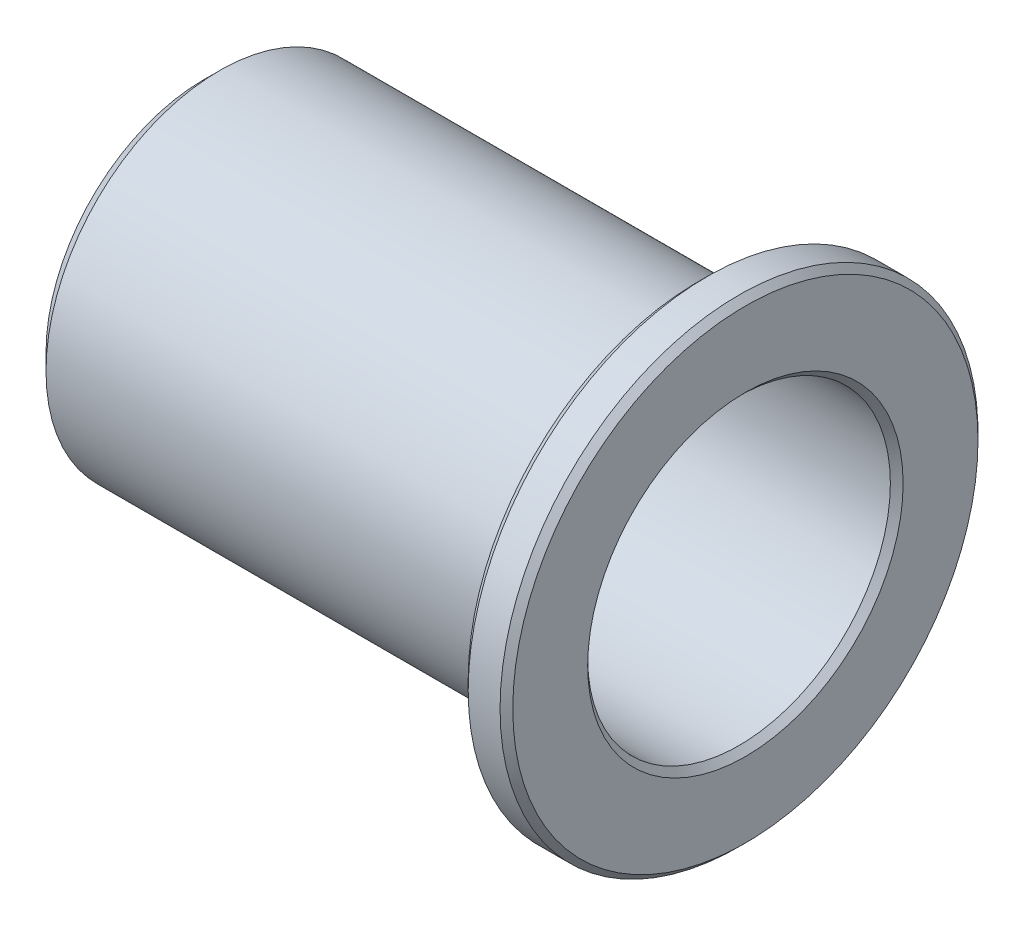
SolidWorks part; units mm, degrees
ref_plane "Спереди" through (0, 0, 0) normal (0, 0, 1) x (1, 0, 0)
ref_plane "Сверху" through (0, 0, 0) normal (0, 1, 0) x (1, 0, 0)
ref_plane "Справа" through (0, 0, 0) normal (1, 0, 0) x (0, 0, -1)
sketch "Эскиз1" plane through (0, 0, 0) normal (0, 0, 1) x (1, 0, 0)
  line L0 (-38.4825, 0) -> (53.8184, 0) construction
  line L18 (-31.1486, 4.75) -> (-31.1486, 4.95)
  line L19 (-14.1486, 4.95) -> (-14.1486, 7.3)
  line L20 (-30.6486, 5.45) -> (-15.6486, 5.45)
  line L21 (-15.6486, 5.45) -> (-15.6486, 7.2)
  line L22 (-15.3486, 7.5) -> (-14.3486, 7.5)
  line L23 (-31.1486, 4.75) -> (-14.3486, 4.75)
  line L24 (-31.1486, 4.95) -> (-30.6486, 5.45)
  line L25 (-15.6486, 7.2) -> (-15.3486, 7.5)
  line L26 (-14.1486, 7.3) -> (-14.3486, 7.5)
  line L27 (-14.3486, 4.75) -> (-14.1486, 4.95)
  point P4 (-31.1486, 5.45)
  point P7 (-14.1486, 7.5)
  point P11 (-15.6486, 7.5)
  point P12 (-14.1486, 4.75)
  dimension "D1" = 17
  dimension "D2" = 15
  dimension "D3" = 10.9
  dimension "D4" = 9.5
  dimension "D5" = 1.5
revolve "Повернуть2" add sketch "Эскиз1" angle 360 about L0
